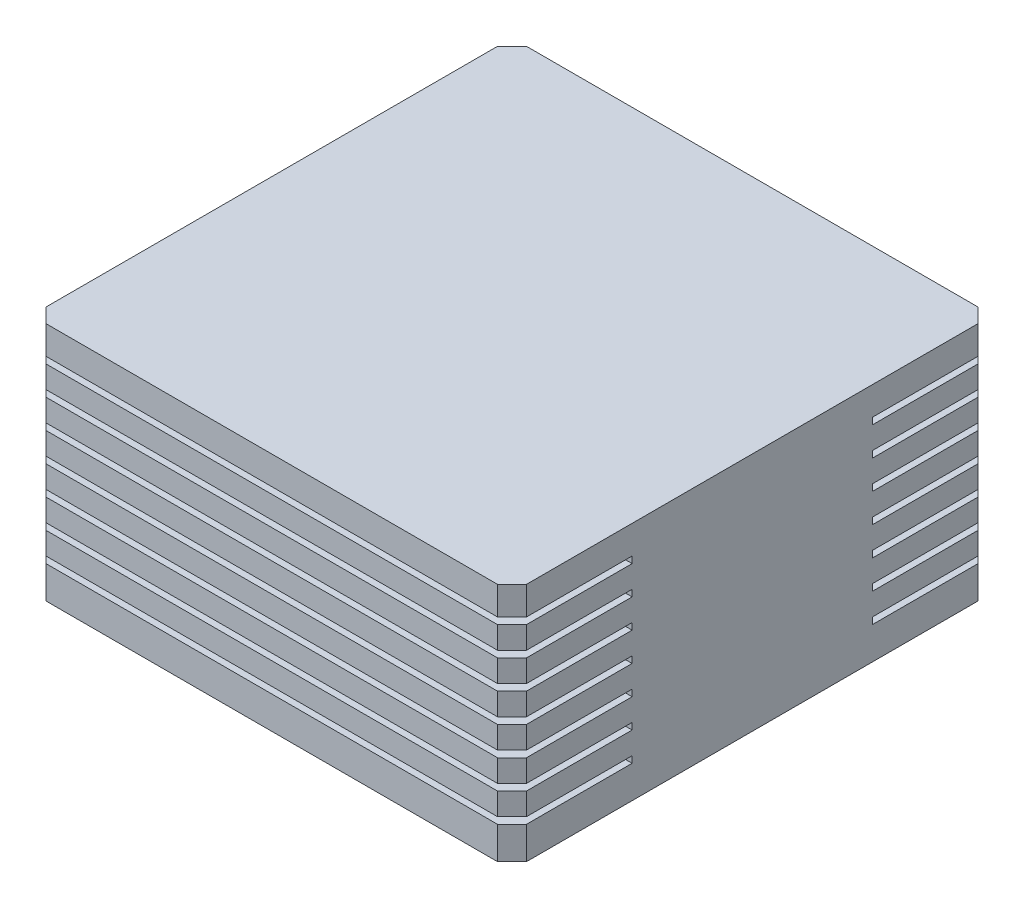
SolidWorks part; units mm, degrees
ref_plane "Front Plane" through (0, 0, 0) normal (0, 0, 1) x (1, 0, 0)
ref_plane "Top Plane" through (0, 0, 0) normal (0, 1, 0) x (1, 0, 0)
ref_plane "Right Plane" through (0, 0, 0) normal (1, 0, 0) x (0, 0, -1)
sketch "Sketch1" plane through (0, 0, 0) normal (0, 1, 0) x (1, 0, 0)
  line L1 (0, 0) -> (100, 0)
  line L2 (0, 0) -> (0, -100)
  line L3 (0, -100) -> (100, -100)
  line L4 (100, 0) -> (100, -100)
  dimension "D1" = 100
  dimension "D2" = 100
extrude "Boss-Extrude1" add sketch "Sketch1" along normal blind 50
chamfer "Chamfer1" distance 3 angle 45 4 edges at (100, 25, 100) (100, 25, 0) (0, 25, 0) (0, 25, 100)
sketch "Sketch3" plane through (0, 0, 0) normal (-1, 0, 0) x (0, 0, 1)
  line L0 (0, 0) -> (0, 50) construction
  line L1 (0, 44.1104) -> (100, 44.1104)
  line L2 (0, 44.1104) -> (0, 42.7413)
  line L3 (0, 42.7413) -> (100, 42.7413)
  line L4 (100, 44.1104) -> (100, 42.7413)
  line L5 (100, 50) -> (100, 0) construction
  line L6 (0, 38.1104) -> (0, 36.7413)
  line L7 (0, 38.1104) -> (100, 38.1104)
  line L8 (100, 38.1104) -> (100, 36.7413)
  line L9 (0, 36.7413) -> (100, 36.7413)
  line L10 (0, 32.1104) -> (0, 30.7413)
  line L11 (0, 32.1104) -> (100, 32.1104)
  line L12 (100, 32.1104) -> (100, 30.7413)
  line L13 (0, 30.7413) -> (100, 30.7413)
  line L14 (0, 26.1104) -> (0, 24.7413)
  line L15 (0, 26.1104) -> (100, 26.1104)
  line L16 (100, 26.1104) -> (100, 24.7413)
  line L17 (0, 24.7413) -> (100, 24.7413)
  line L18 (0, 20.1104) -> (0, 18.7413)
  line L19 (0, 20.1104) -> (100, 20.1104)
  line L20 (100, 20.1104) -> (100, 18.7413)
  line L21 (0, 18.7413) -> (100, 18.7413)
  line L22 (0, 14.1104) -> (0, 12.7413)
  line L23 (0, 14.1104) -> (100, 14.1104)
  line L24 (100, 14.1104) -> (100, 12.7413)
  line L25 (0, 12.7413) -> (100, 12.7413)
  line L26 (0, 8.1104) -> (0, 6.7413)
  line L27 (0, 8.1104) -> (100, 8.1104)
  line L28 (100, 8.1104) -> (100, 6.7413)
  line L29 (0, 6.7413) -> (100, 6.7413)
  dimension "D1" = 7
extrude "Cut-Extrude1" cut sketch "Sketch3" against normal blind 25
sketch "Sketch4" plane through (0, 0, 100) normal (0, 0, 1) x (1, 0, 0)
  line L0 (25, 42.7413) -> (97, 42.7413)
  line L1 (97, 0) -> (97, 50) construction
  line L2 (100, 50) -> (100, 0) construction
  line L3 (25, 44.1104) -> (100, 44.1104)
  line L4 (25, 44.1104) -> (25, 42.7413)
  line L5 (25, 42.7413) -> (100, 42.7413)
  line L6 (100, 44.1104) -> (100, 42.7413)
  line L7 (25, 36.7413) -> (97, 36.7413)
  line L8 (25, 38.1104) -> (25, 36.7413)
  line L9 (25, 38.1104) -> (100, 38.1104)
  line L10 (100, 38.1104) -> (100, 36.7413)
  line L11 (25, 36.7413) -> (100, 36.7413)
  line L12 (25, 30.7413) -> (97, 30.7413)
  line L13 (25, 32.1104) -> (25, 30.7413)
  line L14 (25, 32.1104) -> (100, 32.1104)
  line L15 (100, 32.1104) -> (100, 30.7413)
  line L16 (25, 30.7413) -> (100, 30.7413)
  line L17 (25, 24.7413) -> (97, 24.7413)
  line L18 (25, 26.1104) -> (25, 24.7413)
  line L19 (25, 26.1104) -> (100, 26.1104)
  line L20 (100, 26.1104) -> (100, 24.7413)
  line L21 (25, 24.7413) -> (100, 24.7413)
  line L22 (25, 18.7413) -> (97, 18.7413)
  line L23 (25, 20.1104) -> (25, 18.7413)
  line L24 (25, 20.1104) -> (100, 20.1104)
  line L25 (100, 20.1104) -> (100, 18.7413)
  line L26 (25, 18.7413) -> (100, 18.7413)
  line L27 (25, 12.7413) -> (97, 12.7413)
  line L28 (25, 14.1104) -> (25, 12.7413)
  line L29 (25, 14.1104) -> (100, 14.1104)
  line L30 (100, 14.1104) -> (100, 12.7413)
  line L31 (25, 12.7413) -> (100, 12.7413)
  line L32 (25, 6.7413) -> (97, 6.7413)
  line L33 (25, 8.1104) -> (25, 6.7413)
  line L34 (25, 8.1104) -> (100, 8.1104)
  line L35 (100, 8.1104) -> (100, 6.7413)
  line L36 (25, 6.7413) -> (100, 6.7413)
  line M15 (25, 26.1104) -> (25, 24.7413)
  line M19 (25, 20.1104) -> (25, 18.7413)
  line M23 (25, 14.1104) -> (25, 12.7413)
  line M31 (97, 0) -> (97, 50)
  dimension "D1" = 7
extrude "Cut-Extrude2" cut sketch "Sketch4" against normal blind 25 contours L19 L17 M15 M31 | L24 L22 M19 M31 | L29 L27 M23 M31 | L21 L20 L19 M31 | L26 L25 L24 M31 | L31 L30 L29 M31 | L33 L34 L35 L36 | L13 L14 L15 L16 | L8 L9 L10 L11 | L4 L3 L6 L5
sketch "Sketch5" plane through (0, 0, 0) normal (0, 0, -1) x (-1, 0, 0)
  line L0 (-25, 44.1104) -> (-100, 44.1104)
  line L1 (-100, 0) -> (-100, 50) construction
  line L2 (-25, 38.1104) -> (-100, 38.1104)
  line L4 (-100, 44.1104) -> (-100, 42.7413)
  line L5 (-100, 42.7413) -> (-25, 42.7413)
  line L6 (-25, 44.1104) -> (-25, 42.7413)
  line L7 (-100, 38.1104) -> (-100, 36.7413)
  line L9 (-25, 38.1104) -> (-25, 36.7413)
  line L10 (-100, 36.7413) -> (-25, 36.7413)
  line L11 (-25, 32.1104) -> (-100, 32.1104)
  line L12 (-100, 32.1104) -> (-100, 30.7413)
  line L14 (-25, 32.1104) -> (-25, 30.7413)
  line L15 (-100, 30.7413) -> (-25, 30.7413)
  line L16 (-25, 26.1104) -> (-100, 26.1104)
  line L17 (-100, 26.1104) -> (-100, 24.7413)
  line L19 (-25, 26.1104) -> (-25, 24.7413)
  line L20 (-100, 24.7413) -> (-25, 24.7413)
  line L21 (-25, 20.1104) -> (-100, 20.1104)
  line L22 (-100, 20.1104) -> (-100, 18.7413)
  line L24 (-25, 20.1104) -> (-25, 18.7413)
  line L25 (-100, 18.7413) -> (-25, 18.7413)
  line L26 (-25, 14.1104) -> (-100, 14.1104)
  line L27 (-100, 14.1104) -> (-100, 12.7413)
  line L29 (-25, 14.1104) -> (-25, 12.7413)
  line L30 (-100, 12.7413) -> (-25, 12.7413)
  line L31 (-25, 8.1104) -> (-100, 8.1104)
  line L32 (-100, 8.1104) -> (-100, 6.7413)
  line L34 (-25, 8.1104) -> (-25, 6.7413)
  line L35 (-100, 6.7413) -> (-25, 6.7413)
  dimension "D2" = 1.3691
  dimension "D1" = 7
extrude "Cut-Extrude3" cut sketch "Sketch5" against normal blind 25
